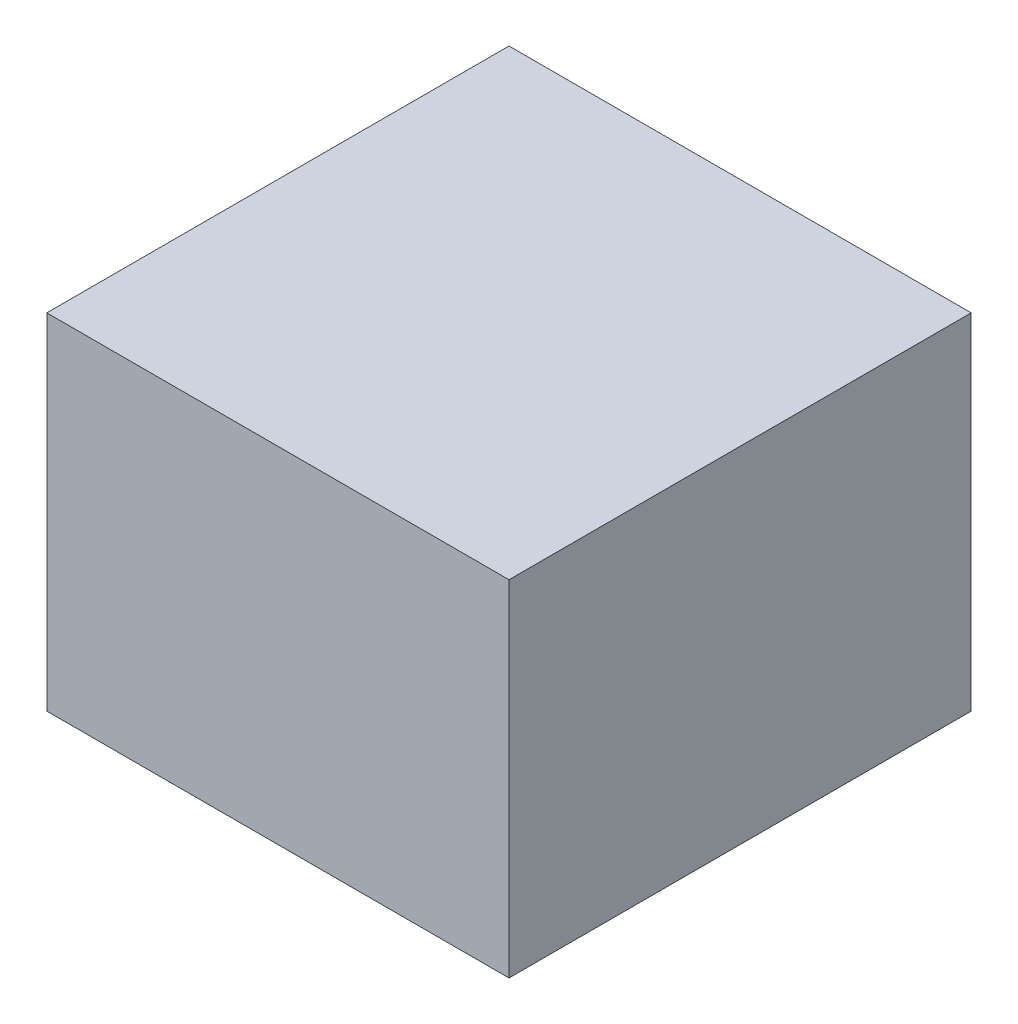
SolidWorks part; units mm, degrees
ref_plane "Front Plane" through (0, 0, 0) normal (0, 0, 1) x (1, 0, 0)
ref_plane "Top Plane" through (0, 0, 0) normal (0, 1, 0) x (1, 0, 0)
ref_plane "Right Plane" through (0, 0, 0) normal (1, 0, 0) x (0, 0, -1)
sketch "Sketch1" plane through (0, 0, 0) normal (0, 1, 0) x (1, 0, 0)
  line L0 (0, -6.7) -> (-6.7, -6.7)
  line L1 (-6.7, -6.7) -> (-6.7, 6.7)
  line L2 (-6.7, 6.7) -> (6.7, 6.7)
  line L3 (6.7, 6.7) -> (6.7, -6.7)
  line L4 (6.7, -6.7) -> (0, -6.7)
  circle A0 centre (0, 0) radius 4.7
  circle A1 centre (0, 0) radius 6.7 construction
  dimension "D1" = 9.4
  dimension "D2" = 2
extrude "Boss-Extrude1" add sketch "Sketch1" along normal blind 6
sketch "Sketch2" plane through (0, 6, 0) normal (0, 1, 0) x (1, 0, 0)
  line L1 (-6.7, -6.7) -> (6.7, -6.7)
  line L2 (-6.7, -6.7) -> (-6.7, 6.7)
  line L3 (-6.7, 6.7) -> (6.7, 6.7)
  line L4 (6.7, -6.7) -> (6.7, 6.7)
extrude "Boss-Extrude2" add sketch "Sketch2" along normal blind 4
